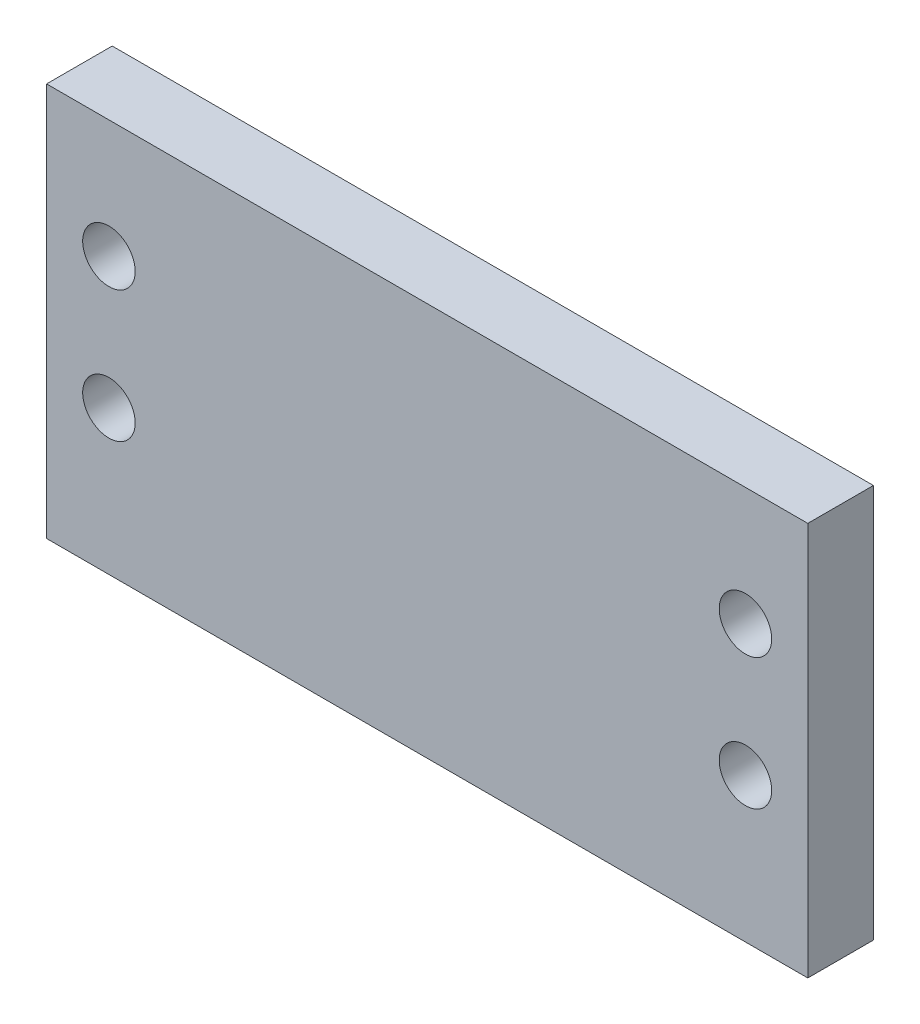
SolidWorks part; units mm, degrees
ref_plane "Front Plane" through (0, 0, 0) normal (0, 0, 1) x (1, 0, 0)
ref_plane "Top Plane" through (0, 0, 0) normal (0, 1, 0) x (1, 0, 0)
ref_plane "Right Plane" through (0, 0, 0) normal (1, 0, 0) x (0, 0, -1)
sketch "Sketch1" plane through (0, 0, 0) normal (0, 0, 1) x (1, 0, 0)
  line L1 (0, 0) -> (-58, 0)
  line L2 (0, 0) -> (0, 30)
  line L3 (0, 30) -> (-58, 30)
  line L4 (-58, 0) -> (-58, 30)
  circle A0 centre (-53.25, 21) radius 2
  circle A1 centre (-53.25, 11) radius 2
  circle A2 centre (-4.75, 21) radius 2
  circle A3 centre (-4.75, 11) radius 2
  dimension "D4" = 4
  dimension "D5" = 9
  dimension "D8" = 4
  dimension "D11" = 4
  dimension "D13" = 4
  dimension "D1" = 58
  dimension "D2" = 30
  dimension "D3" = 4.75
  dimension "D6" = 10
  dimension "D7" = 4.75
  dimension "D9" = 10
  dimension "D10" = 9
  dimension "D12" = 4.75
  dimension "D14" = 4.75
extrude "Boss-Extrude1" add sketch "Sketch1" along normal blind 5
